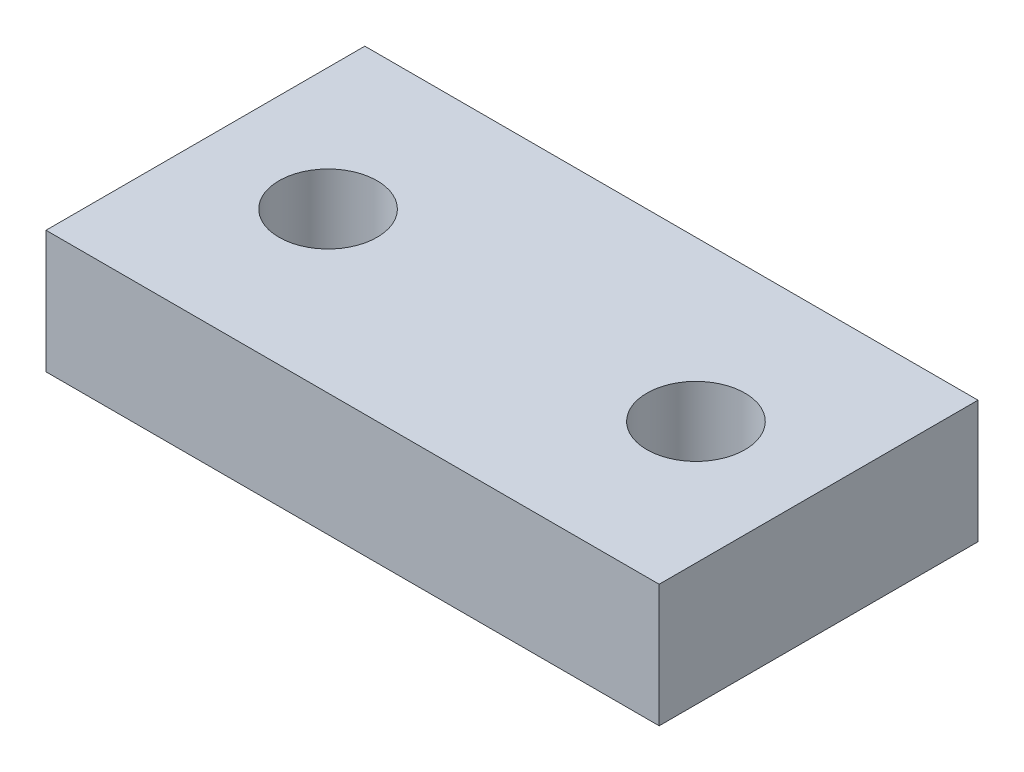
SolidWorks part; units mm, degrees
ref_plane "Front Plane" through (0, 0, 0) normal (0, 0, 1) x (1, 0, 0)
ref_plane "Top Plane" through (0, 0, 0) normal (0, 1, 0) x (1, 0, 0)
ref_plane "Right Plane" through (0, 0, 0) normal (1, 0, 0) x (0, 0, -1)
sketch "Sketch1" plane through (0, 0, 0) normal (0, 1, 0) x (1, 0, 0)
  line L1 (-12.5, 6.5) -> (12.5, 6.5)
  line L2 (-12.5, 6.5) -> (-12.5, -6.5)
  line L3 (-12.5, -6.5) -> (12.5, -6.5)
  line L4 (12.5, 6.5) -> (12.5, -6.5)
  line L5 (-12.5, 6.5) -> (12.5, -6.5) construction
  line L6 (-12.5, -6.5) -> (12.5, 6.5) construction
  circle A0 centre (-7.5, 0) radius 2
  circle A1 centre (7.5, 0) radius 2
  point P0 (0, 0)
  dimension "D3" = 4
  dimension "D4" = 4
  dimension "D1" = 25
  dimension "D2" = 13
  dimension "D5" = 7.5
  dimension "D6" = 7.5
extrude "Boss-Extrude1" add sketch "Sketch1" along normal blind 5
